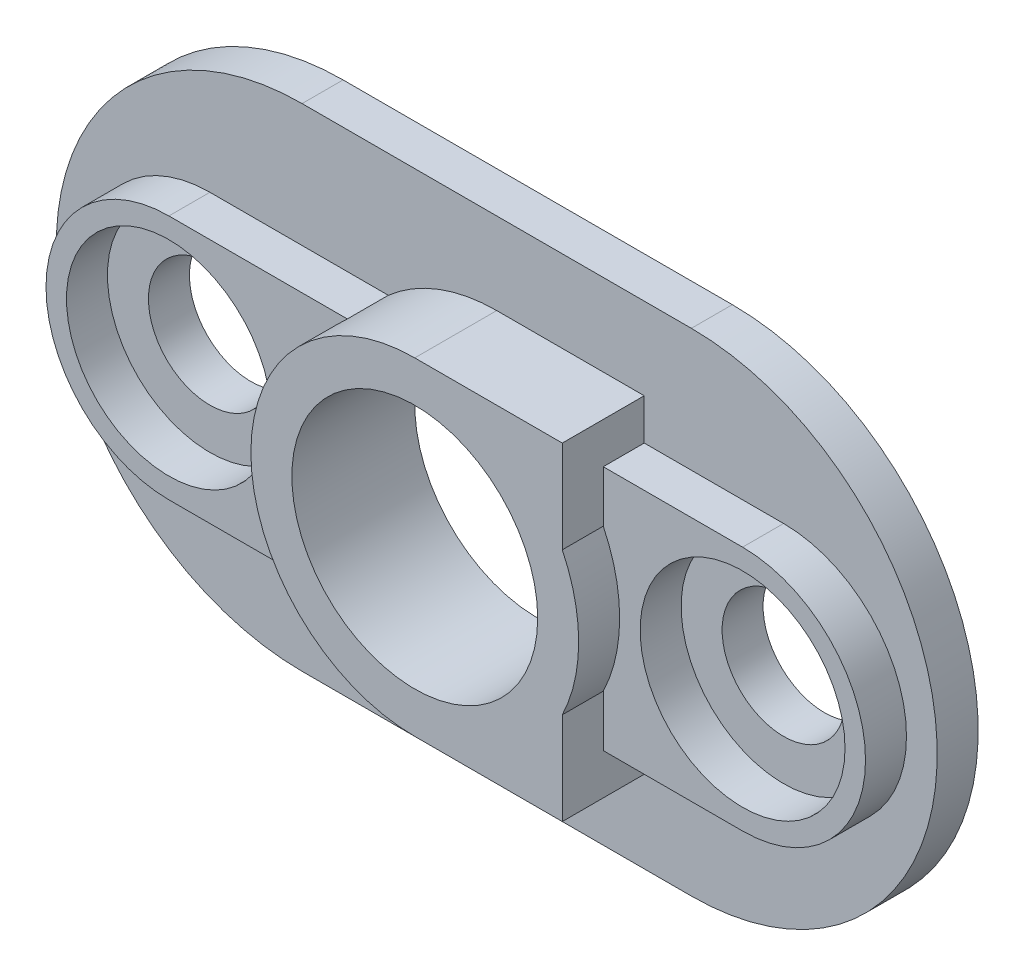
SolidWorks part; units mm, degrees
ref_plane "Face" through (0, 0, 0) normal (0, 0, 1) x (1, 0, 0)
ref_plane "Dessus" through (0, 0, 0) normal (0, 1, 0) x (1, 0, 0)
ref_plane "Droite" through (0, 0, 0) normal (1, 0, 0) x (0, 0, -1)
sketch "Esquisse1" plane through (0, 0, 0) normal (0, 0, 1) x (1, 0, 0)
  line L0 (-57.0491, 33.907) -> (-38.0491, 33.907)
  line L2 (-38.0491, 9.907) -> (-57.0491, 9.907)
  arc A0 (-38.0491, 9.907) -> (-38.0491, 33.907) centre (-38.0491, 21.907) ccw
  arc A1 (-57.0491, 33.907) -> (-57.0491, 9.907) centre (-57.0491, 21.907) ccw
extrude "Extrusion1" add sketch "Esquisse1" along normal blind 2
sketch "Esquisse2" plane through (0, 0, 2) normal (0, 0, 1) x (1, 0, 0)
  line L0 (-61.5491, 27.907) -> (-33.5491, 27.907)
  line L1 (-57.0491, 33.907) -> (-38.0491, 33.907) construction
  line L2 (-33.5491, 15.907) -> (-61.5491, 15.907)
  arc A0 (-33.5491, 15.907) -> (-33.5491, 27.907) centre (-33.5491, 21.907) ccw
  arc A1 (-61.5491, 27.907) -> (-61.5491, 15.907) centre (-61.5491, 21.907) ccw
  dimension "D1" = 12
  dimension "D2" = 28
  dimension "D3" = 4.5
  dimension "D4" = 6
extrude "Extrusion4" add sketch "Esquisse2" along normal blind 2
sketch "Esquisse4" plane through (0, 0, 2) normal (0, 0, 1) x (1, 0, 0)
  line L0 (-47.5493, 29.907) -> (-40.3493, 29.907)
  line L1 (-40.3493, 29.907) -> (-40.3493, 25.3942)
  line L2 (-40.3493, 13.907) -> (-47.5493, 13.907)
  line L3 (-40.3493, 18.4199) -> (-40.3493, 13.907)
  line L4 (-57.0491, 9.907) -> (-38.0491, 9.907) construction
  arc A0 (-40.3493, 18.4199) -> (-40.3493, 25.3942) centre (-47.5493, 21.907) ccw
  arc A1 (-47.5493, 29.907) -> (-47.5493, 13.907) centre (-47.5493, 21.907) ccw
  dimension "D1" = 16
  dimension "D2" = 4
extrude "Extrusion5" add sketch "Esquisse4" along normal blind 4
sketch "Esquisse3" plane through (0, 0, 4) normal (0, 0, 1) x (1, 0, 0)
  line L8 (-61.5491, 27.907) -> (-33.5491, 27.907) construction
  circle A0 centre (-47.5491, 21.907) radius 6
  arc A3 (-61.5491, 27.907) -> (-61.5491, 15.907) centre (-61.5491, 21.907) ccw construction
  dimension "D7" = 12
  dimension "D1" = 14
  dimension "D5" = 6
extrude "Enlèv. mat.-Extru.1" cut sketch "Esquisse3" against normal mid plane 10
sketch "Esquisse5" plane through (0, 0, 4) normal (0, 0, 1) x (1, 0, 0)
  circle A0 centre (-61.5491, 21.907) radius 3
  circle A1 centre (-33.5491, 21.907) radius 3
  arc A2 (-33.5491, 15.907) -> (-33.5491, 27.907) centre (-33.5491, 21.907) ccw construction
  arc A3 (-61.5491, 27.907) -> (-61.5491, 15.907) centre (-61.5491, 21.907) ccw construction
  dimension "D1" = 6
  dimension "D2" = 6
extrude "Enlèv. mat.-Extru.2" cut sketch "Esquisse5" against normal through all
sketch "Esquisse6" plane through (0, 0, 4) normal (0, 0, 1) x (1, 0, 0)
  circle A0 centre (-61.5491, 21.907) radius 5
  circle A1 centre (-33.5491, 21.907) radius 5
  circle A2 centre (-33.5491, 21.907) radius 3 construction
  circle A3 centre (-61.5491, 21.907) radius 3 construction
  dimension "D1" = 10
  dimension "D2" = 10
extrude "Enlèv. mat.-Extru.3" cut sketch "Esquisse6" against normal blind 2
